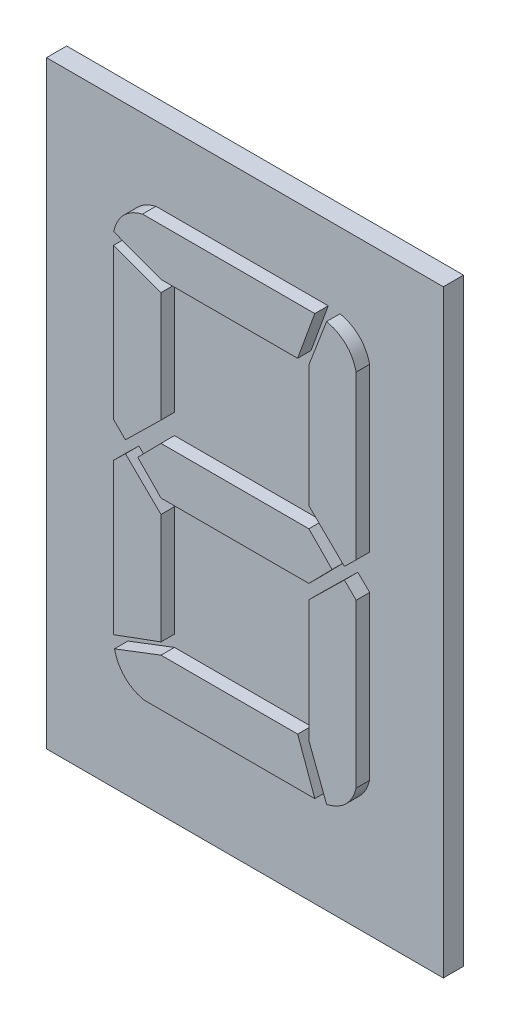
SolidWorks part; units mm, degrees
material "Laiton"
ref_plane "Plan de face" through (0, 0, 0) normal (0, 0, 1) x (1, 0, 0)
ref_plane "Plan de dessus" through (0, 0, 0) normal (0, 1, 0) x (1, 0, 0)
ref_plane "Plan de droite" through (0, 0, 0) normal (1, 0, 0) x (0, 0, -1)
sketch "Esquisse1" plane through (0, 0, 0) normal (0, 0, 1) x (1, 0, 0)
  line L1 (0, 0) -> (5.9, 0)
  line L2 (0, 0) -> (0, 8.9)
  line L3 (0, 8.9) -> (5.9, 8.9)
  line L4 (5.9, 0) -> (5.9, 8.9)
  dimension "D1" = 5.9
  dimension "D2" = 8.9
extrude "Boss.-Extru.1" add sketch "Esquisse1" along normal blind 0.3
sketch "Esquisse2" plane through (0, 0, 0.3) normal (0, 0, 1) x (1, 0, 0)
  text T0 "8" font "Digital-7" height in points 24
extrude "Boss.-Extru.2" add sketch "Esquisse2" along normal blind 0.2
